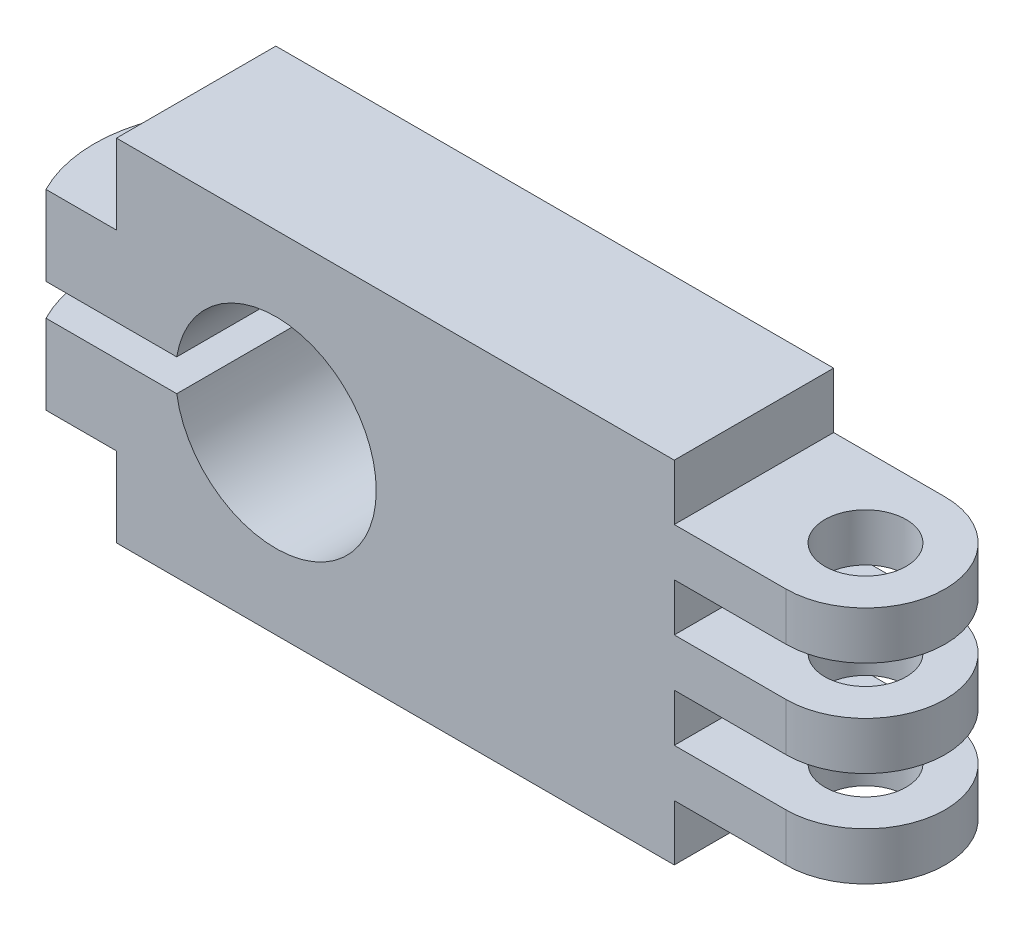
SolidWorks part; units mm, degrees
ref_plane "前视基准面" through (0, 0, 0) normal (0, 0, 1) x (1, 0, 0)
ref_plane "上视基准面" through (0, 0, 0) normal (0, 1, 0) x (1, 0, 0)
ref_plane "右视基准面" through (0, 0, 0) normal (1, 0, 0) x (0, 0, -1)
sketch "草图1" plane through (0, 0, 0) normal (0, 0, 1) x (1, 0, 0)
  line L0 (0, 0) -> (35, 0)
  line L1 (35, 0) -> (35, -3.5)
  line L2 (35, -3.5) -> (47, -3.5)
  line L3 (47, -3.5) -> (47, -6.5)
  line L4 (47, -6.5) -> (35, -6.5)
  line L5 (35, -6.5) -> (35, -9.5)
  line L6 (35, -9.5) -> (47, -9.5)
  line L7 (47, -9.5) -> (47, -12.5)
  line L8 (47, -12.5) -> (35, -12.5)
  line L9 (35, -12.5) -> (35, -15.5)
  line L10 (35, -15.5) -> (47, -15.5)
  line L11 (47, -15.5) -> (47, -18.5)
  line L12 (47, -18.5) -> (35, -18.5)
  line L13 (35, -18.5) -> (35, -22)
  line L14 (35, -22) -> (0, -22)
  line L15 (0, -22) -> (0, -17)
  line L16 (0, -17) -> (-10, -17)
  line L17 (-10, -17) -> (-10, -12)
  line L21 (-10, -10) -> (0, -10)
  line L22 (-10, -10) -> (-10, -5)
  line L26 (0, -10) -> (0, -12)
  line L27 (0, -12) -> (-10, -12)
  line L28 (-10, -5) -> (0, -5)
  line L29 (0, -5) -> (0, 0)
extrude "凸台-拉伸1" add sketch "草图1" along normal blind 10 contours L29 L0 L1 L2 L3 L4 L5 L6 L7 L8 L9 L10 L11 L12 L13 L14 L15 L16 L17 L27 L26 L21 L22 L28
sketch "草图2" plane through (0, -3.5, 0) normal (0, 1, 0) x (1, 0, 0)
  line L0 (47, -5) -> (42, -5) construction
  line L1 (47, -10) -> (47, 0) construction
  circle A0 centre (42, -5) radius 2.55
extrude "切除-拉伸1" cut sketch "草图2" against normal blind 19
sketch "草图3" plane through (0, -3.5, 0) normal (0, 1, 0) x (1, 0, 0)
  line L0 (42, 0) -> (35, 0)
  line L1 (35, -10) -> (35, 0) construction
  line L2 (35, 0) -> (35, 1.3629)
  line L3 (35, 1.3629) -> (53.3289, 1.3629)
  line L4 (53.3289, 1.3629) -> (53.3289, -13.8132)
  line L5 (53.3289, -13.8132) -> (35, -13.8132)
  line L6 (35, -13.8132) -> (35, -10)
  line L7 (35, -10) -> (42, -10)
  arc A0 (42, -10) -> (42, 0) centre (42, -5) ccw
extrude "切除-拉伸2" cut sketch "草图3" against normal blind 19
sketch "草图5" plane through (0, 0, 10) normal (0, 0, 1) x (1, 0, 0)
  line L0 (0, -11) -> (10, -11) construction
  line L1 (0, -10) -> (0, -12) construction
  line L3 (0, -10) -> (10, -10)
  line L4 (0, -10) -> (0, -12)
  line L5 (0, -12) -> (10, -12)
  line L6 (10, -10) -> (10, -12)
extrude "切除-拉伸4" cut sketch "草图5" against normal blind 19
sketch "草图6" plane through (0, 0, 10) normal (0, 0, 1) x (1, 0, 0)
  line L0 (10, -12) -> (10, -10) construction
  circle A0 centre (10, -11) radius 6.3
extrude "切除-拉伸5" cut sketch "草图6" against normal blind 19
sketch "草图7" plane through (0, -5, 0) normal (0, 1, 0) x (1, 0, 0)
  line L0 (-10, 0) -> (0, 0) construction
  line L1 (-10, -10) -> (0, -10) construction
  line L2 (-4.4228, -10) -> (-4.4228, -16.2455)
  line L3 (-4.4228, -16.2455) -> (-15.2417, -16.2455)
  line L4 (-15.2417, -16.2455) -> (-15.2417, 3.3262)
  line L5 (-15.2417, 3.3262) -> (-3, 3.3262)
  line L6 (-3, 3.3262) -> (-3, 0)
  arc A0 (-3, 0) -> (-4.4228, -10) centre (3.3167, -6) ccw
extrude "切除-拉伸6" cut sketch "草图7" against normal blind 19
sketch "草图8" plane through (0, -5, 0) normal (0, 1, 0) x (1, 0, 0)
  circle A1 centre (-2.5, -6) radius 1
extrude "切除-拉伸7" cut sketch "草图8" against normal blind 18
